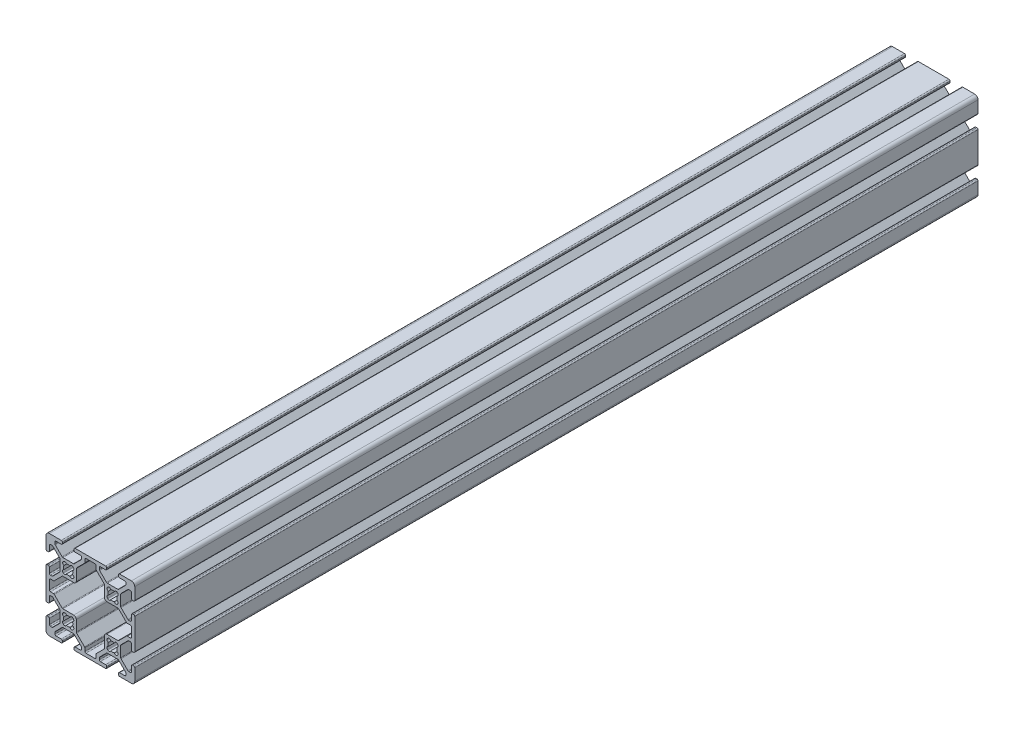
SolidWorks part; units mm, degrees
material "6105-T5 Aluminum"
ref_plane "Front Plane" through (0, 0, 0) normal (0, 0, 1) x (1, 0, 0)
ref_plane "Top Plane" through (0, 0, 0) normal (0, 1, 0) x (1, 0, 0)
ref_plane "Right Plane" through (0, 0, 0) normal (1, 0, 0) x (0, 0, -1)
sketch "Sketch1" plane through (0, 0, 0) normal (0, 0, 1) x (1, 0, 0)
  line L0 (-2.1249, 17.6955) -> (-2.3045, 17.8751)
  line L1 (-2.3045, 22.1249) -> (-2.1249, 22.3045)
  line L2 (2.1249, 22.3045) -> (2.3045, 22.1249)
  line L3 (2.3045, 17.8751) -> (2.1249, 17.6955)
  line L4 (-22.1249, 17.6955) -> (-22.3045, 17.8751)
  line L5 (-22.3045, 22.1249) -> (-22.1249, 22.3045)
  line L6 (-17.8751, 22.3045) -> (-17.6955, 22.1249)
  line L7 (-17.6955, 17.8751) -> (-17.8751, 17.6955)
  line L8 (-2.1249, -2.3045) -> (-2.3045, -2.1249)
  line L9 (-2.3045, 2.1249) -> (-2.1249, 2.3045)
  line L10 (2.1249, 2.3045) -> (2.3045, 2.1249)
  line L11 (2.3045, -2.1249) -> (2.1249, -2.3045)
  line L12 (-12.505, -7.992) -> (-12.505, -6.6448)
  line L13 (-12.6538, -6.2856) -> (-16.1962, -2.7431)
  line L14 (-16.345, -2.3839) -> (-16.345, 2.512)
  line L15 (-17.488, 3.655) -> (-22.3839, 3.655)
  line L16 (-22.7431, 3.8038) -> (-26.2856, 7.3462)
  line L17 (-26.6448, 7.495) -> (-27.992, 7.495)
  line L18 (-28.5, 8.003) -> (-28.5, 11.997)
  line L19 (-27.992, 12.505) -> (-26.6448, 12.505)
  line L20 (-26.2856, 12.6538) -> (-22.7431, 16.1962)
  line L21 (-22.3839, 16.345) -> (-17.488, 16.345)
  line L22 (-16.345, 17.488) -> (-16.345, 22.3839)
  line L23 (-16.1962, 22.7431) -> (-12.6538, 26.2856)
  line L24 (-12.505, 26.6448) -> (-12.505, 27.992)
  line L25 (-11.997, 28.5) -> (-8.003, 28.5)
  line L26 (-7.495, 27.992) -> (-7.495, 26.6448)
  line L27 (-7.3462, 26.2856) -> (-3.8038, 22.7431)
  line L28 (-3.655, 22.3839) -> (-3.655, 17.488)
  line L29 (-2.512, 16.345) -> (2.3839, 16.345)
  line L30 (2.7431, 16.1962) -> (6.2856, 12.6538)
  line L31 (6.6448, 12.505) -> (7.992, 12.505)
  line L32 (8.5, 11.997) -> (8.5, 8.003)
  line L33 (7.992, 7.495) -> (6.6448, 7.495)
  line L34 (6.2856, 7.3462) -> (2.7431, 3.8038)
  line L35 (2.3839, 3.655) -> (-2.512, 3.655)
  line L36 (-3.655, 2.512) -> (-3.655, -2.3839)
  line L37 (-3.8038, -2.7431) -> (-7.3462, -6.2856)
  line L38 (-7.495, -6.6448) -> (-7.495, -7.992)
  line L39 (-8.003, -8.5) -> (-11.997, -8.5)
  line L40 (-22.1249, -2.3045) -> (-22.3045, -2.1249)
  line L41 (-22.3045, 2.1249) -> (-22.1249, 2.3045)
  line L42 (-17.8751, 2.3045) -> (-17.6955, 2.1249)
  line L43 (-17.6955, -2.1249) -> (-17.8751, -2.3045)
  line L44 (-22.3839, -3.655) -> (-17.6161, -3.655)
  line L45 (-17.2569, -3.8038) -> (-14.1538, -6.9069)
  line L46 (-14.005, -7.2661) -> (-14.005, -7.992)
  line L47 (-14.513, -8.5) -> (-16.862, -8.5)
  line L48 (-17.37, -9.008) -> (-17.37, -9.492)
  line L49 (-16.862, -10) -> (-3.138, -10)
  line L50 (-2.63, -9.492) -> (-2.63, -9.008)
  line L51 (-3.138, -8.5) -> (-5.487, -8.5)
  line L52 (-5.995, -7.992) -> (-5.995, -7.2661)
  line L53 (-5.8462, -6.9069) -> (-2.7431, -3.8038)
  line L54 (-2.3839, -3.655) -> (2.3839, -3.655)
  line L55 (2.7431, -3.8038) -> (5.8462, -6.9069)
  line L56 (5.995, -7.2661) -> (5.995, -7.992)
  line L57 (5.487, -8.5) -> (3.138, -8.5)
  line L58 (2.63, -9.008) -> (2.63, -9.492)
  line L59 (3.138, -10) -> (8.5, -10)
  line L60 (10, -8.5) -> (10, -3.138)
  line L61 (9.492, -2.63) -> (9.008, -2.63)
  line L62 (8.5, -3.138) -> (8.5, -5.487)
  line L63 (7.992, -5.995) -> (7.2661, -5.995)
  line L64 (6.9069, -5.8462) -> (3.8038, -2.7431)
  line L65 (3.655, -2.3839) -> (3.655, 2.3839)
  line L66 (3.8038, 2.7431) -> (6.9069, 5.8462)
  line L67 (7.2661, 5.995) -> (7.992, 5.995)
  line L68 (8.5, 5.487) -> (8.5, 3.138)
  line L69 (9.008, 2.63) -> (9.492, 2.63)
  line L70 (10, 3.138) -> (10, 16.862)
  line L71 (9.492, 17.37) -> (9.008, 17.37)
  line L72 (8.5, 16.862) -> (8.5, 14.513)
  line L73 (7.992, 14.005) -> (7.2661, 14.005)
  line L74 (6.9069, 14.1538) -> (3.8038, 17.2569)
  line L75 (3.655, 17.6161) -> (3.655, 22.3839)
  line L76 (3.8038, 22.7431) -> (6.9069, 25.8462)
  line L77 (7.2661, 25.995) -> (7.992, 25.995)
  line L78 (8.5, 25.487) -> (8.5, 23.138)
  line L79 (9.008, 22.63) -> (9.492, 22.63)
  line L80 (10, 23.138) -> (10, 28.5)
  line L81 (8.5, 30) -> (3.138, 30)
  line L82 (2.63, 29.492) -> (2.63, 29.008)
  line L83 (3.138, 28.5) -> (5.487, 28.5)
  line L84 (5.995, 27.992) -> (5.995, 27.2661)
  line L85 (5.8462, 26.9069) -> (2.7431, 23.8038)
  line L86 (2.3839, 23.655) -> (-2.3839, 23.655)
  line L87 (-2.7431, 23.8038) -> (-5.8462, 26.9069)
  line L88 (-5.995, 27.2661) -> (-5.995, 27.992)
  line L89 (-5.487, 28.5) -> (-3.138, 28.5)
  line L90 (-2.63, 29.008) -> (-2.63, 29.492)
  line L91 (-3.138, 30) -> (-16.862, 30)
  line L92 (-17.37, 29.492) -> (-17.37, 29.008)
  line L93 (-16.862, 28.5) -> (-14.513, 28.5)
  line L94 (-14.005, 27.992) -> (-14.005, 27.2661)
  line L95 (-14.1538, 26.9069) -> (-17.2569, 23.8038)
  line L96 (-17.6161, 23.655) -> (-22.3839, 23.655)
  line L97 (-22.7431, 23.8038) -> (-25.8462, 26.9069)
  line L98 (-25.995, 27.2661) -> (-25.995, 27.992)
  line L99 (-25.487, 28.5) -> (-23.138, 28.5)
  line L100 (-22.63, 29.008) -> (-22.63, 29.492)
  line L101 (-23.138, 30) -> (-28.5, 30)
  line L102 (-30, 28.5) -> (-30, 23.138)
  line L103 (-29.492, 22.63) -> (-29.008, 22.63)
  line L104 (-28.5, 23.138) -> (-28.5, 25.487)
  line L105 (-27.992, 25.995) -> (-27.2661, 25.995)
  line L106 (-26.9069, 25.8462) -> (-23.8038, 22.7431)
  line L107 (-23.655, 22.3839) -> (-23.655, 17.6161)
  line L108 (-23.8038, 17.2569) -> (-26.9069, 14.1538)
  line L109 (-27.2661, 14.005) -> (-27.992, 14.005)
  line L110 (-28.5, 14.513) -> (-28.5, 16.862)
  line L111 (-29.008, 17.37) -> (-29.492, 17.37)
  line L112 (-30, 16.862) -> (-30, 3.138)
  line L113 (-29.492, 2.63) -> (-29.008, 2.63)
  line L114 (-28.5, 3.138) -> (-28.5, 5.487)
  line L115 (-27.992, 5.995) -> (-27.2661, 5.995)
  line L116 (-26.9069, 5.8462) -> (-23.8038, 2.7431)
  line L117 (-23.655, 2.3839) -> (-23.655, -2.3839)
  line L118 (-23.8038, -2.7431) -> (-26.9069, -5.8462)
  line L119 (-27.2661, -5.995) -> (-27.992, -5.995)
  line L120 (-28.5, -5.487) -> (-28.5, -3.138)
  line L121 (-29.008, -2.63) -> (-29.492, -2.63)
  line L122 (-30, -3.138) -> (-30, -8.5)
  line L123 (-28.5, -10) -> (-23.138, -10)
  line L124 (-22.63, -9.492) -> (-22.63, -9.008)
  line L125 (-23.138, -8.5) -> (-25.487, -8.5)
  line L126 (-25.995, -7.992) -> (-25.995, -7.2661)
  line L127 (-25.8462, -6.9069) -> (-22.7431, -3.8038)
  arc A0 (-1.9351, 19.196) -> (-2.3045, 17.8751) centre (-1.748, 18.4316) ccw
  arc A1 (-1.9351, 20.804) -> (-1.9351, 19.196) centre (0, 20) ccw
  arc A2 (-2.3045, 22.1249) -> (-1.9351, 20.804) centre (-1.748, 21.5684) ccw
  arc A3 (-0.804, 21.9351) -> (-2.1249, 22.3045) centre (-1.5684, 21.748) ccw
  arc A4 (0.804, 21.9351) -> (-0.804, 21.9351) centre (0, 20) ccw
  arc A5 (2.1249, 22.3045) -> (0.804, 21.9351) centre (1.5684, 21.748) ccw
  arc A6 (1.9351, 20.804) -> (2.3045, 22.1249) centre (1.748, 21.5684) ccw
  arc A7 (1.9351, 19.196) -> (1.9351, 20.804) centre (0, 20) ccw
  arc A8 (2.3045, 17.8751) -> (1.9351, 19.196) centre (1.748, 18.4316) ccw
  arc A9 (0.804, 18.0649) -> (2.1249, 17.6955) centre (1.5684, 18.252) ccw
  arc A10 (-0.804, 18.0649) -> (0.804, 18.0649) centre (0, 20) ccw
  arc A11 (-2.1249, 17.6955) -> (-0.804, 18.0649) centre (-1.5684, 18.252) ccw
  arc A12 (-21.9351, 19.196) -> (-22.3045, 17.8751) centre (-21.748, 18.4316) ccw
  arc A13 (-21.9351, 20.804) -> (-21.9351, 19.196) centre (-20, 20) ccw
  arc A14 (-22.3045, 22.1249) -> (-21.9351, 20.804) centre (-21.748, 21.5684) ccw
  arc A15 (-20.804, 21.9351) -> (-22.1249, 22.3045) centre (-21.5684, 21.748) ccw
  arc A16 (-19.196, 21.9351) -> (-20.804, 21.9351) centre (-20, 20) ccw
  arc A17 (-17.8751, 22.3045) -> (-19.196, 21.9351) centre (-18.4316, 21.748) ccw
  arc A18 (-18.0649, 20.804) -> (-17.6955, 22.1249) centre (-18.252, 21.5684) ccw
  arc A19 (-18.0649, 19.196) -> (-18.0649, 20.804) centre (-20, 20) ccw
  arc A20 (-17.6955, 17.8751) -> (-18.0649, 19.196) centre (-18.252, 18.4316) ccw
  arc A21 (-19.196, 18.0649) -> (-17.8751, 17.6955) centre (-18.4316, 18.252) ccw
  arc A22 (-20.804, 18.0649) -> (-19.196, 18.0649) centre (-20, 20) ccw
  arc A23 (-22.1249, 17.6955) -> (-20.804, 18.0649) centre (-21.5684, 18.252) ccw
  arc A24 (-1.9351, -0.804) -> (-2.3045, -2.1249) centre (-1.748, -1.5684) ccw
  arc A25 (-1.9351, 0.804) -> (-1.9351, -0.804) centre (0, 0) ccw
  arc A26 (-2.3045, 2.1249) -> (-1.9351, 0.804) centre (-1.748, 1.5684) ccw
  arc A27 (-0.804, 1.9351) -> (-2.1249, 2.3045) centre (-1.5684, 1.748) ccw
  arc A28 (0.804, 1.9351) -> (-0.804, 1.9351) centre (0, 0) ccw
  arc A29 (2.1249, 2.3045) -> (0.804, 1.9351) centre (1.5684, 1.748) ccw
  arc A30 (1.9351, 0.804) -> (2.3045, 2.1249) centre (1.748, 1.5684) ccw
  arc A31 (1.9351, -0.804) -> (1.9351, 0.804) centre (0, 0) ccw
  arc A32 (2.3045, -2.1249) -> (1.9351, -0.804) centre (1.748, -1.5684) ccw
  arc A33 (0.804, -1.9351) -> (2.1249, -2.3045) centre (1.5684, -1.748) ccw
  arc A34 (-0.804, -1.9351) -> (0.804, -1.9351) centre (0, 0) ccw
  arc A35 (-2.1249, -2.3045) -> (-0.804, -1.9351) centre (-1.5684, -1.748) ccw
  arc A36 (-12.505, -7.992) -> (-11.997, -8.5) centre (-11.997, -7.992) ccw
  arc A37 (-12.505, -6.6448) -> (-12.6538, -6.2856) centre (-13.013, -6.6448) ccw
  arc A38 (-16.345, -2.3839) -> (-16.1962, -2.7431) centre (-15.837, -2.3839) ccw
  arc A39 (-16.345, 2.512) -> (-17.488, 3.655) centre (-17.488, 2.512) ccw
  arc A40 (-22.7431, 3.8038) -> (-22.3839, 3.655) centre (-22.3839, 4.163) ccw
  arc A41 (-26.2856, 7.3462) -> (-26.6448, 7.495) centre (-26.6448, 6.987) ccw
  arc A42 (-28.5, 8.003) -> (-27.992, 7.495) centre (-27.992, 8.003) ccw
  arc A43 (-27.992, 12.505) -> (-28.5, 11.997) centre (-27.992, 11.997) ccw
  arc A44 (-26.6448, 12.505) -> (-26.2856, 12.6538) centre (-26.6448, 13.013) ccw
  arc A45 (-22.3839, 16.345) -> (-22.7431, 16.1962) centre (-22.3839, 15.837) ccw
  arc A46 (-17.488, 16.345) -> (-16.345, 17.488) centre (-17.488, 17.488) ccw
  arc A47 (-16.1962, 22.7431) -> (-16.345, 22.3839) centre (-15.837, 22.3839) ccw
  arc A48 (-12.6538, 26.2856) -> (-12.505, 26.6448) centre (-13.013, 26.6448) ccw
  arc A49 (-11.997, 28.5) -> (-12.505, 27.992) centre (-11.997, 27.992) ccw
  arc A50 (-7.495, 27.992) -> (-8.003, 28.5) centre (-8.003, 27.992) ccw
  arc A51 (-7.495, 26.6448) -> (-7.3462, 26.2856) centre (-6.987, 26.6448) ccw
  arc A52 (-3.655, 22.3839) -> (-3.8038, 22.7431) centre (-4.163, 22.3839) ccw
  arc A53 (-3.655, 17.488) -> (-2.512, 16.345) centre (-2.512, 17.488) ccw
  arc A54 (2.7431, 16.1962) -> (2.3839, 16.345) centre (2.3839, 15.837) ccw
  arc A55 (6.2856, 12.6538) -> (6.6448, 12.505) centre (6.6448, 13.013) ccw
  arc A56 (8.5, 11.997) -> (7.992, 12.505) centre (7.992, 11.997) ccw
  arc A57 (7.992, 7.495) -> (8.5, 8.003) centre (7.992, 8.003) ccw
  arc A58 (6.6448, 7.495) -> (6.2856, 7.3462) centre (6.6448, 6.987) ccw
  arc A59 (2.3839, 3.655) -> (2.7431, 3.8038) centre (2.3839, 4.163) ccw
  arc A60 (-2.512, 3.655) -> (-3.655, 2.512) centre (-2.512, 2.512) ccw
  arc A61 (-3.8038, -2.7431) -> (-3.655, -2.3839) centre (-4.163, -2.3839) ccw
  arc A62 (-7.3462, -6.2856) -> (-7.495, -6.6448) centre (-6.987, -6.6448) ccw
  arc A63 (-8.003, -8.5) -> (-7.495, -7.992) centre (-8.003, -7.992) ccw
  arc A64 (-21.9351, -0.804) -> (-22.3045, -2.1249) centre (-21.748, -1.5684) ccw
  arc A65 (-21.9351, 0.804) -> (-21.9351, -0.804) centre (-20, 0) ccw
  arc A66 (-22.3045, 2.1249) -> (-21.9351, 0.804) centre (-21.748, 1.5684) ccw
  arc A67 (-20.804, 1.9351) -> (-22.1249, 2.3045) centre (-21.5684, 1.748) ccw
  arc A68 (-19.196, 1.9351) -> (-20.804, 1.9351) centre (-20, 0) ccw
  arc A69 (-17.8751, 2.3045) -> (-19.196, 1.9351) centre (-18.4316, 1.748) ccw
  arc A70 (-18.0649, 0.804) -> (-17.6955, 2.1249) centre (-18.252, 1.5684) ccw
  arc A71 (-18.0649, -0.804) -> (-18.0649, 0.804) centre (-20, 0) ccw
  arc A72 (-17.6955, -2.1249) -> (-18.0649, -0.804) centre (-18.252, -1.5684) ccw
  arc A73 (-19.196, -1.9351) -> (-17.8751, -2.3045) centre (-18.4316, -1.748) ccw
  arc A74 (-20.804, -1.9351) -> (-19.196, -1.9351) centre (-20, 0) ccw
  arc A75 (-22.1249, -2.3045) -> (-20.804, -1.9351) centre (-21.5684, -1.748) ccw
  arc A76 (-22.3839, -3.655) -> (-22.7431, -3.8038) centre (-22.3839, -4.163) ccw
  arc A77 (-17.2569, -3.8038) -> (-17.6161, -3.655) centre (-17.6161, -4.163) ccw
  arc A78 (-14.005, -7.2661) -> (-14.1538, -6.9069) centre (-14.513, -7.2661) ccw
  arc A79 (-14.513, -8.5) -> (-14.005, -7.992) centre (-14.513, -7.992) ccw
  arc A80 (-16.862, -8.5) -> (-17.37, -9.008) centre (-16.862, -9.008) ccw
  arc A81 (-17.37, -9.492) -> (-16.862, -10) centre (-16.862, -9.492) ccw
  arc A82 (-3.138, -10) -> (-2.63, -9.492) centre (-3.138, -9.492) ccw
  arc A83 (-2.63, -9.008) -> (-3.138, -8.5) centre (-3.138, -9.008) ccw
  arc A84 (-5.995, -7.992) -> (-5.487, -8.5) centre (-5.487, -7.992) ccw
  arc A85 (-5.8462, -6.9069) -> (-5.995, -7.2661) centre (-5.487, -7.2661) ccw
  arc A86 (-2.3839, -3.655) -> (-2.7431, -3.8038) centre (-2.3839, -4.163) ccw
  arc A87 (2.7431, -3.8038) -> (2.3839, -3.655) centre (2.3839, -4.163) ccw
  arc A88 (5.995, -7.2661) -> (5.8462, -6.9069) centre (5.487, -7.2661) ccw
  arc A89 (5.487, -8.5) -> (5.995, -7.992) centre (5.487, -7.992) ccw
  arc A90 (3.138, -8.5) -> (2.63, -9.008) centre (3.138, -9.008) ccw
  arc A91 (2.63, -9.492) -> (3.138, -10) centre (3.138, -9.492) ccw
  arc A92 (8.5, -10) -> (10, -8.5) centre (8.5, -8.5) ccw
  arc A93 (10, -3.138) -> (9.492, -2.63) centre (9.492, -3.138) ccw
  arc A94 (9.008, -2.63) -> (8.5, -3.138) centre (9.008, -3.138) ccw
  arc A95 (7.992, -5.995) -> (8.5, -5.487) centre (7.992, -5.487) ccw
  arc A96 (6.9069, -5.8462) -> (7.2661, -5.995) centre (7.2661, -5.487) ccw
  arc A97 (3.655, -2.3839) -> (3.8038, -2.7431) centre (4.163, -2.3839) ccw
  arc A98 (3.8038, 2.7431) -> (3.655, 2.3839) centre (4.163, 2.3839) ccw
  arc A99 (7.2661, 5.995) -> (6.9069, 5.8462) centre (7.2661, 5.487) ccw
  arc A100 (8.5, 5.487) -> (7.992, 5.995) centre (7.992, 5.487) ccw
  arc A101 (8.5, 3.138) -> (9.008, 2.63) centre (9.008, 3.138) ccw
  arc A102 (9.492, 2.63) -> (10, 3.138) centre (9.492, 3.138) ccw
  arc A103 (10, 16.862) -> (9.492, 17.37) centre (9.492, 16.862) ccw
  arc A104 (9.008, 17.37) -> (8.5, 16.862) centre (9.008, 16.862) ccw
  arc A105 (7.992, 14.005) -> (8.5, 14.513) centre (7.992, 14.513) ccw
  arc A106 (6.9069, 14.1538) -> (7.2661, 14.005) centre (7.2661, 14.513) ccw
  arc A107 (3.655, 17.6161) -> (3.8038, 17.2569) centre (4.163, 17.6161) ccw
  arc A108 (3.8038, 22.7431) -> (3.655, 22.3839) centre (4.163, 22.3839) ccw
  arc A109 (7.2661, 25.995) -> (6.9069, 25.8462) centre (7.2661, 25.487) ccw
  arc A110 (8.5, 25.487) -> (7.992, 25.995) centre (7.992, 25.487) ccw
  arc A111 (8.5, 23.138) -> (9.008, 22.63) centre (9.008, 23.138) ccw
  arc A112 (9.492, 22.63) -> (10, 23.138) centre (9.492, 23.138) ccw
  arc A113 (10, 28.5) -> (8.5, 30) centre (8.5, 28.5) ccw
  arc A114 (3.138, 30) -> (2.63, 29.492) centre (3.138, 29.492) ccw
  arc A115 (2.63, 29.008) -> (3.138, 28.5) centre (3.138, 29.008) ccw
  arc A116 (5.995, 27.992) -> (5.487, 28.5) centre (5.487, 27.992) ccw
  arc A117 (5.8462, 26.9069) -> (5.995, 27.2661) centre (5.487, 27.2661) ccw
  arc A118 (2.3839, 23.655) -> (2.7431, 23.8038) centre (2.3839, 24.163) ccw
  arc A119 (-2.7431, 23.8038) -> (-2.3839, 23.655) centre (-2.3839, 24.163) ccw
  arc A120 (-5.995, 27.2661) -> (-5.8462, 26.9069) centre (-5.487, 27.2661) ccw
  arc A121 (-5.487, 28.5) -> (-5.995, 27.992) centre (-5.487, 27.992) ccw
  arc A122 (-3.138, 28.5) -> (-2.63, 29.008) centre (-3.138, 29.008) ccw
  arc A123 (-2.63, 29.492) -> (-3.138, 30) centre (-3.138, 29.492) ccw
  arc A124 (-16.862, 30) -> (-17.37, 29.492) centre (-16.862, 29.492) ccw
  arc A125 (-17.37, 29.008) -> (-16.862, 28.5) centre (-16.862, 29.008) ccw
  arc A126 (-14.005, 27.992) -> (-14.513, 28.5) centre (-14.513, 27.992) ccw
  arc A127 (-14.1538, 26.9069) -> (-14.005, 27.2661) centre (-14.513, 27.2661) ccw
  arc A128 (-17.6161, 23.655) -> (-17.2569, 23.8038) centre (-17.6161, 24.163) ccw
  arc A129 (-22.7431, 23.8038) -> (-22.3839, 23.655) centre (-22.3839, 24.163) ccw
  arc A130 (-25.995, 27.2661) -> (-25.8462, 26.9069) centre (-25.487, 27.2661) ccw
  arc A131 (-25.487, 28.5) -> (-25.995, 27.992) centre (-25.487, 27.992) ccw
  arc A132 (-23.138, 28.5) -> (-22.63, 29.008) centre (-23.138, 29.008) ccw
  arc A133 (-22.63, 29.492) -> (-23.138, 30) centre (-23.138, 29.492) ccw
  arc A134 (-28.5, 30) -> (-30, 28.5) centre (-28.5, 28.5) ccw
  arc A135 (-30, 23.138) -> (-29.492, 22.63) centre (-29.492, 23.138) ccw
  arc A136 (-29.008, 22.63) -> (-28.5, 23.138) centre (-29.008, 23.138) ccw
  arc A137 (-27.992, 25.995) -> (-28.5, 25.487) centre (-27.992, 25.487) ccw
  arc A138 (-26.9069, 25.8462) -> (-27.2661, 25.995) centre (-27.2661, 25.487) ccw
  arc A139 (-23.655, 22.3839) -> (-23.8038, 22.7431) centre (-24.163, 22.3839) ccw
  arc A140 (-23.8038, 17.2569) -> (-23.655, 17.6161) centre (-24.163, 17.6161) ccw
  arc A141 (-27.2661, 14.005) -> (-26.9069, 14.1538) centre (-27.2661, 14.513) ccw
  arc A142 (-28.5, 14.513) -> (-27.992, 14.005) centre (-27.992, 14.513) ccw
  arc A143 (-28.5, 16.862) -> (-29.008, 17.37) centre (-29.008, 16.862) ccw
  arc A144 (-29.492, 17.37) -> (-30, 16.862) centre (-29.492, 16.862) ccw
  arc A145 (-30, 3.138) -> (-29.492, 2.63) centre (-29.492, 3.138) ccw
  arc A146 (-29.008, 2.63) -> (-28.5, 3.138) centre (-29.008, 3.138) ccw
  arc A147 (-27.992, 5.995) -> (-28.5, 5.487) centre (-27.992, 5.487) ccw
  arc A148 (-26.9069, 5.8462) -> (-27.2661, 5.995) centre (-27.2661, 5.487) ccw
  arc A149 (-23.655, 2.3839) -> (-23.8038, 2.7431) centre (-24.163, 2.3839) ccw
  arc A150 (-23.8038, -2.7431) -> (-23.655, -2.3839) centre (-24.163, -2.3839) ccw
  arc A151 (-27.2661, -5.995) -> (-26.9069, -5.8462) centre (-27.2661, -5.487) ccw
  arc A152 (-28.5, -5.487) -> (-27.992, -5.995) centre (-27.992, -5.487) ccw
  arc A153 (-28.5, -3.138) -> (-29.008, -2.63) centre (-29.008, -3.138) ccw
  arc A154 (-29.492, -2.63) -> (-30, -3.138) centre (-29.492, -3.138) ccw
  arc A155 (-30, -8.5) -> (-28.5, -10) centre (-28.5, -8.5) ccw
  arc A156 (-23.138, -10) -> (-22.63, -9.492) centre (-23.138, -9.492) ccw
  arc A157 (-22.63, -9.008) -> (-23.138, -8.5) centre (-23.138, -9.008) ccw
  arc A158 (-25.995, -7.992) -> (-25.487, -8.5) centre (-25.487, -7.992) ccw
  arc A159 (-25.8462, -6.9069) -> (-25.995, -7.2661) centre (-25.487, -7.2661) ccw
extrude "Extrude1" add sketch "Sketch1" against normal blind 380
